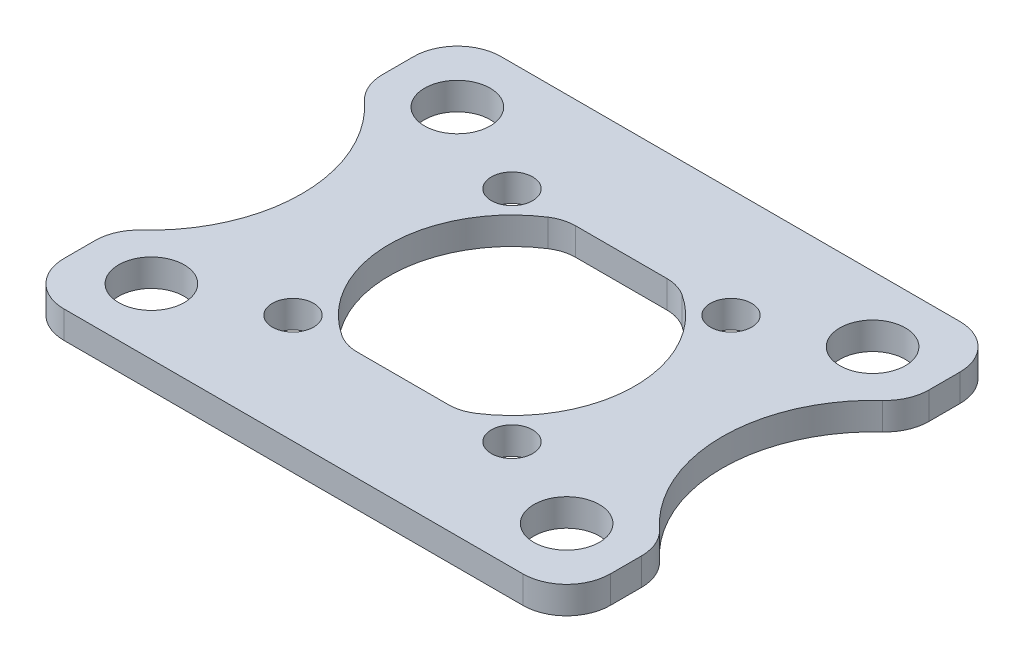
SolidWorks part; units mm, degrees
material "Alum Plate"
ref_plane "Front Plane" through (0, 0, 0) normal (0, 0, 1) x (1, 0, 0)
ref_plane "Top Plane" through (0, 0, 0) normal (0, 1, 0) x (1, 0, 0)
ref_plane "Right Plane" through (0, 0, 0) normal (1, 0, 0) x (0, 0, -1)
sketch "Sketch1" plane through (0, 0, 0) normal (0, 1, 0) x (1, 0, 0)
  line L0 (-6.364, 6.364) -> (6.364, -6.364) construction
  line L1 (-15.875, -12.7) -> (15.875, -12.7)
  line L2 (-15.875, -12.7) -> (-15.875, 12.7)
  line L3 (-15.875, 12.7) -> (15.875, 12.7)
  line L4 (15.875, -12.7) -> (15.875, 12.7)
  line L5 (-15.875, -12.7) -> (15.875, 12.7) construction
  line L6 (-15.875, 12.7) -> (15.875, -12.7) construction
  line L7 (-6.364, -6.364) -> (6.364, 6.364) construction
  line L8 (-6.364, 6.364) -> (-6.364, 12.7) construction
  line L9 (6.364, 6.364) -> (6.364, 12.7) construction
  line L10 (-15.875, 8.89) -> (-12.065, 8.89) construction
  line L11 (-12.065, 8.89) -> (-12.065, 12.7) construction
  line L12 (12.065, 12.7) -> (12.065, 8.89) construction
  line L13 (12.065, 8.89) -> (15.875, 8.89) construction
  line L14 (-12.065, 8.89) -> (0, 0) construction
  line L15 (12.065, -8.89) -> (12.065, -12.7) construction
  line L16 (12.065, -8.89) -> (15.875, -8.89) construction
  line L17 (-12.065, -12.7) -> (-12.065, -8.89) construction
  line L18 (-12.065, -8.89) -> (-15.875, -8.89) construction
  line L19 (-12.065, -8.89) -> (12.065, -8.89) construction
  circle A0 centre (0, 0) radius 7.1374
  circle A1 centre (-6.364, -6.364) radius 1.2
  circle A2 centre (-6.364, 6.364) radius 1.2
  circle A3 centre (6.364, 6.364) radius 1.2
  circle A4 centre (6.364, -6.364) radius 1.2
  circle A5 centre (-12.065, -8.89) radius 1.905
  circle A6 centre (-12.065, 8.89) radius 1.905
  circle A7 centre (12.065, 8.89) radius 1.905
  circle A8 centre (12.065, -8.89) radius 1.905
  circle A9 centre (0, 0) radius 10.9982 construction
  point P0 (0, 0)
  point P18 (0, 0)
  point P19 (0, 0)
  dimension "D1" = 14.2748
  dimension "D2" = 2.4
  dimension "D3" = 9
  dimension "D4" = 3.81
  dimension "D8" = 21.9964
  dimension "D5" = 25.4
  dimension "D6" = 31.75
  dimension "D7" = 3.81
extrude "Boss-Extrude1" add sketch "Sketch1" along normal blind 1.5875
sketch "Sketch3" plane through (0, 1.5875, 0) normal (0, 1, 0) x (1, 0, 0)
  line L0 (-3.2588, 6.35) -> (3.2588, 6.35)
  line L2 (3.2588, -6.35) -> (-3.2588, -6.35)
  arc A0 (-3.2588, -6.35) -> (3.2588, -6.35) centre (0, 0) ccw
  circle A1 centre (0, 0) radius 7.1374 construction
  arc A2 (3.2588, 6.35) -> (-3.2588, 6.35) centre (0, 0) ccw
  dimension "D1" = 12.7
extrude "Boss-Extrude3" add sketch "Sketch3" against normal through all
sketch "Sketch4" plane through (0, 0, 0) normal (0, -1, 0) x (1, 0, 0)
  line L0 (-21.04, 0) -> (0, 0) construction
  line L1 (0, 0) -> (21.04, 0) construction
  line L2 (-15.875, -12.7) -> (-15.875, 12.7) construction
  line L3 (15.875, 12.7) -> (15.875, -12.7) construction
  line L4 (-12.2174, 0) -> (-7.1374, 0) construction
  line L5 (-15.875, 7.1527) -> (-15.875, -7.1527)
  line L6 (15.875, -7.1527) -> (15.875, 7.1527)
  line L7 (-14.7719, 6.2088) -> (-12.065, 8.89) construction
  arc A0 (-15.875, 7.1527) -> (-15.875, -7.1527) centre (-21.04, 0) cw
  arc A1 (15.875, 7.1527) -> (15.875, -7.1527) centre (21.04, 0) ccw
  arc A2 (-3.2588, 6.35) -> (-3.2588, -6.35) centre (0, 0) ccw construction
  dimension "D1" = 3.81
  dimension "D2" = 5.08
extrude "Cut-Extrude1" cut sketch "Sketch4" against normal through all
fillet "Fillet3" radius 2.54 8 edges at (-15.875, 0.7937, 7.1527) (-15.875, 0.7937, -7.1527) (-15.875, 0.7937, -12.7) (15.875, 0.7937, -12.7) (15.875, 0.7937, -7.1527) (15.875, 0.7937, 7.1527) (15.875, 0.7937, 12.7) (-15.875, 0.7937, 12.7)
fillet "Fillet2" radius 2.286 4 edges at (-3.2588, 0.7937, -6.35) (3.2588, 0.7937, -6.35) (3.2588, 0.7937, 6.35) (-3.2588, 0.7937, 6.35)
